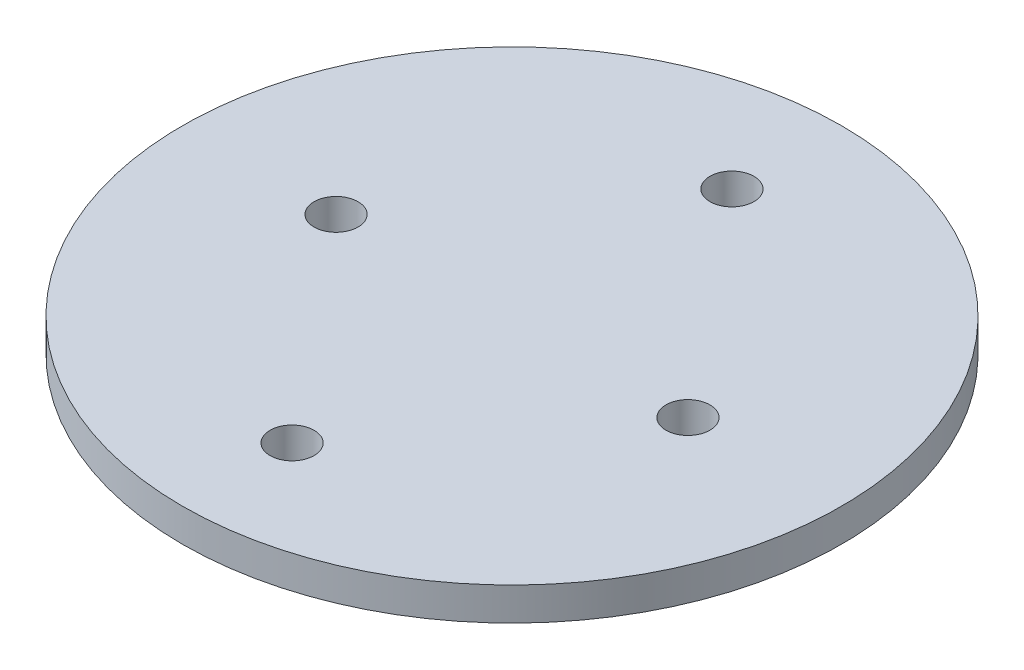
SolidWorks part; units mm, degrees
ref_plane "Front Plane" through (0, 0, 0) normal (0, 0, 1) x (1, 0, 0)
ref_plane "Top Plane" through (0, 0, 0) normal (0, 1, 0) x (1, 0, 0)
ref_plane "Right Plane" through (0, 0, 0) normal (1, 0, 0) x (0, 0, -1)
sketch "Sketch1" plane through (0, 0, 0) normal (0, 1, 0) x (1, 0, 0)
  circle A0 centre (0, 0) radius 47.575
  dimension "D1" = 95.15
extrude "Boss-Extrude1" add sketch "Sketch1" along normal blind 4.7625
sketch "Sketch2" plane through (0, 4.7625, 0) normal (0, 1, 0) x (1, 0, 0)
  circle A0 centre (25.4, 0) radius 3.175
  circle A1 centre (-25.4, 0) radius 3.175
  circle A2 centre (0, 31.75) radius 3.175
  circle A3 centre (0, -31.75) radius 3.175
  dimension "D1" = 6.35
  dimension "D2" = 6.35
  dimension "D3" = 6.35
  dimension "D4" = 6.35
  dimension "D5" = 25.4
  dimension "D6" = 25.4
  dimension "D7" = 31.75
  dimension "D8" = 31.75
extrude "Cut-Extrude1" cut sketch "Sketch2" against normal through all
